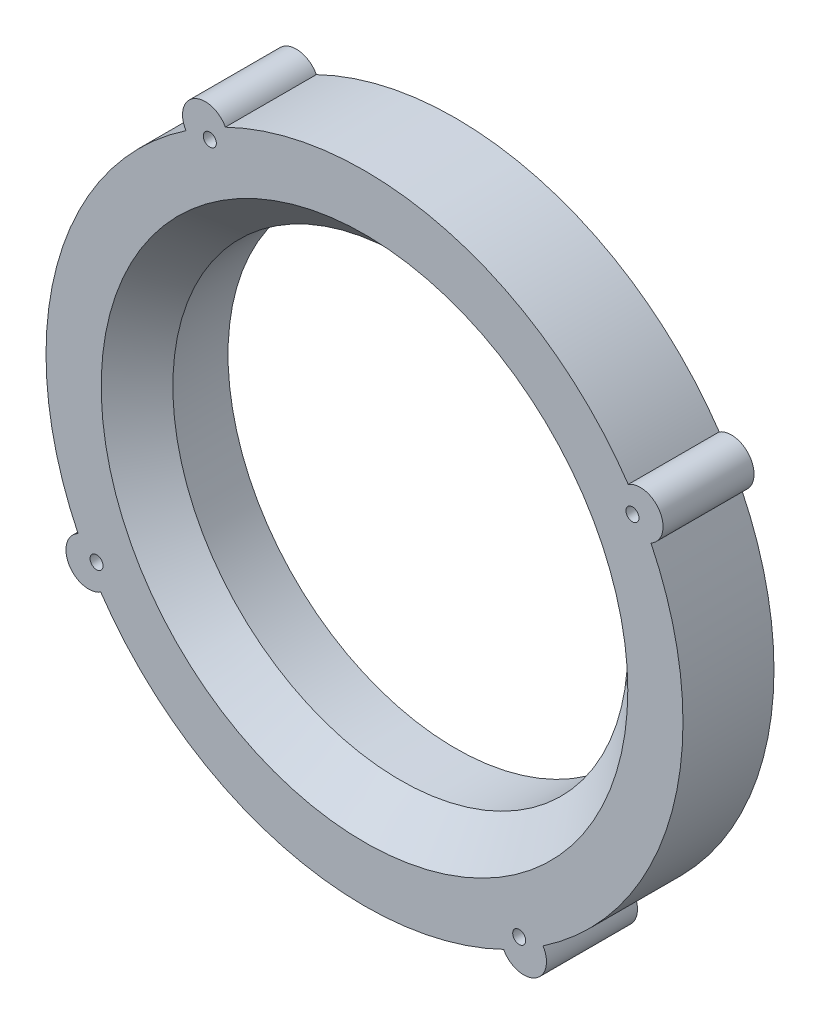
SolidWorks part; units mm, degrees
material "6061-T6 (SS)"
ref_plane "Front Plane" through (0, 0, 0) normal (0, 0, 1) x (1, 0, 0)
ref_plane "Top Plane" through (0, 0, 0) normal (0, 1, 0) x (1, 0, 0)
ref_plane "Right Plane" through (0, 0, 0) normal (1, 0, 0) x (0, 0, -1)
sketch "Sketch1" plane through (0, 0, 0) normal (0, 0, 1) x (1, 0, 0)
  line L0 (0, 0) -> (88.9, 0) construction
  line L1 (0, 0) -> (76.9897, 44.45) construction
  line L2 (0, 0) -> (76.9897, -44.45) construction
  line L3 (0, 0) -> (0, -88.9) construction
  line L4 (0, 0) -> (-76.9897, -44.45) construction
  line L5 (0, 0) -> (-76.9897, 44.45) construction
  line L6 (0, 0) -> (0, 88.9) construction
  circle A0 centre (0, 0) radius 88.9
  circle A1 centre (0, 0) radius 63.5
  circle A13 centre (76.9897, 44.45) radius 6.35
  circle A14 centre (44.45, -76.9897) radius 6.35
  circle A15 centre (0, 0) radius 88.9
  circle A16 centre (-76.9897, -44.45) radius 6.35
  circle A17 centre (0, 0) radius 88.9
  circle A18 centre (-44.45, 76.9897) radius 6.35
  circle A19 centre (0, 0) radius 88.9
  point P14 (0, 0)
  point P20 (0, 0)
  point P36 (0, 0)
  dimension "D1" = 177.8
  dimension "D2" = 127
  dimension "D5" = 4
  dimension "D3" = 30
  dimension "D4" = 6
extrude "Boss-Extrude1" add sketch "Sketch1" along normal blind 25.4
chamfer "Chamfer1" distance 10 angle 45 1 edges at (63.5, 0, 25.4)
sketch "Sketch3" plane through (0, 0, 25.4) normal (0, 0, 1) x (1, 0, 0)
  line L0 (0, 0) -> (74.79, 43.18) construction
  line L1 (0, 0) -> (86.36, 0) construction
  circle A7 centre (0, 0) radius 86.36
  circle A15 centre (74.79, 43.18) radius 1.8161
  circle A16 centre (43.18, -74.79) radius 1.8161
  circle A17 centre (0, 0) radius 86.36
  circle A18 centre (-74.79, -43.18) radius 1.8161
  circle A19 centre (0, 0) radius 86.36
  circle A20 centre (-43.18, 74.79) radius 1.8161
  circle A21 centre (0, 0) radius 86.36
  point P15 (0, 0)
  point P17 (0, 0)
  point P20 (0, 0)
  dimension "D1" = 172.72
  dimension "D3" = 4
  dimension "D4" = 3.6322
  dimension "D2" = 30
extrude "Cut-Extrude1" cut sketch "Sketch3" against normal through all contours A19 A20 | A19 A20 | A7 A15 | A7 A15 | A7 A16 | A7 A16 | A17 A18 | A17 A18
